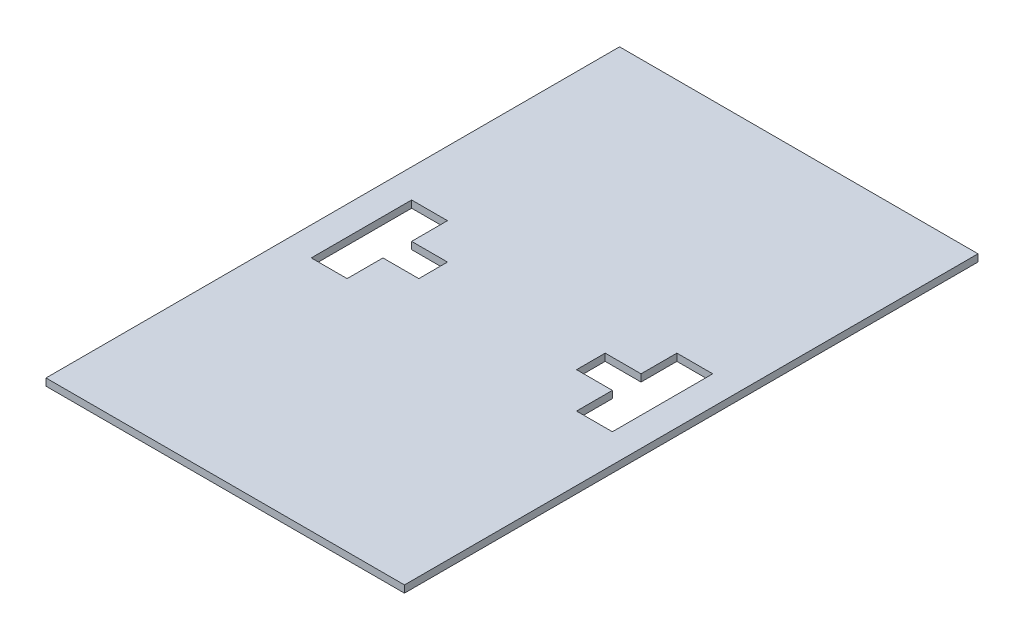
SolidWorks part; units mm, degrees
ref_plane "Front Plane" through (0, 0, 0) normal (0, 0, 1) x (1, 0, 0)
ref_plane "Top Plane" through (0, 0, 0) normal (0, 1, 0) x (1, 0, 0)
ref_plane "Right Plane" through (0, 0, 0) normal (1, 0, 0) x (0, 0, -1)
sketch "Sketch1" plane through (0, 0, 0) normal (0, 1, 0) x (1, 0, 0)
  line L1 (250, -400) -> (-250, -400)
  line L2 (250, -400) -> (250, 400)
  line L3 (250, 400) -> (-250, 400)
  line L4 (-250, -400) -> (-250, 400)
  line L5 (250, -400) -> (-250, 400) construction
  line L6 (250, 400) -> (-250, -400) construction
  point P0 (0, 0)
  dimension "D1" = 500
  dimension "D2" = 800
extrude "Boss-Extrude1" add sketch "Sketch1" along normal blind 10
sketch "Sketch2" plane through (0, 10, 0) normal (0, 1, 0) x (1, 0, 0)
  line L0 (-250, 400) -> (-250, -400) construction
  line L1 (-160, -70) -> (-210, -70)
  line L3 (-160, 70) -> (-210, 70)
  line L4 (-210, -70) -> (-210, 70)
  line L5 (-160, -70) -> (-210, 70) construction
  line L6 (-160, 70) -> (-210, -70) construction
  line L7 (-160, 70) -> (-160, 20)
  line L8 (-110, -20) -> (-160, -20)
  line L9 (-110, -20) -> (-110, 20)
  line L10 (-110, 20) -> (-160, 20)
  line L12 (-110, -20) -> (-160, 20) construction
  line L13 (-110, 20) -> (-160, -20) construction
  line L14 (-160, -20) -> (-160, -70)
  point P0 (-185, 0)
  point P8 (-135, 0)
  dimension "D1" = 50
  dimension "D2" = 140
  dimension "D3" = 40
  dimension "D4" = 50
  dimension "D5" = 40
extrude "Cut-Extrude1" cut sketch "Sketch2" against normal blind 10
mirror "Mirror1" about plane through (0, 0, 0) normal (1, 0, 0) of "Cut-Extrude1"
